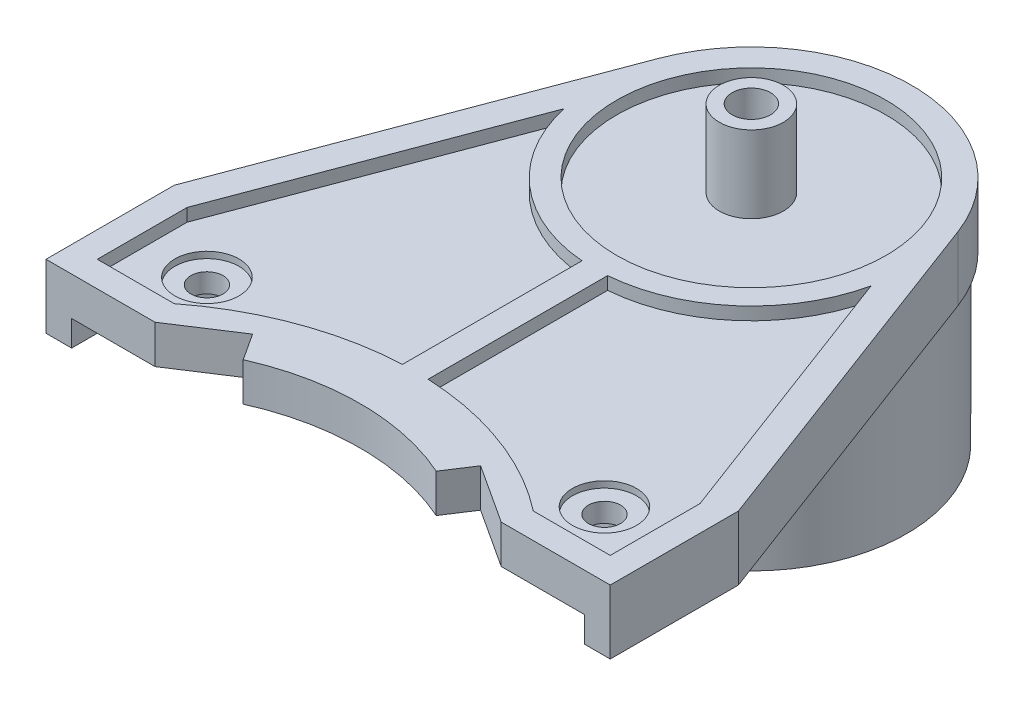
SolidWorks part; units mm, degrees
material "ABS"
ref_plane "Front Plane" through (0, 0, 0) normal (0, 0, 1) x (1, 0, 0)
ref_plane "Top Plane" through (0, 0, 0) normal (0, 1, 0) x (1, 0, 0)
ref_plane "Right Plane" through (0, 0, 0) normal (1, 0, 0) x (0, 0, -1)
sketch "Sketch1" plane through (0, 0, 0) normal (0, 1, 0) x (1, 0, 0)
  line L0 (-22, -33.0049) -> (-13.5, -33.0049)
  line L1 (-13.5, -33.0049) -> (13.5, -33.0049) construction
  line L2 (-22, -33.0049) -> (-22, -23.0049)
  line L3 (0, -30.5) -> (0, 12.5)
  line L4 (-13.5, -33.0049) -> (-8.8902, -30.0049)
  line L5 (0, -55) -> (0, 55) construction
  line L6 (-8.8902, -30.0049) -> (-7.5266, -32.1003)
  line L7 (-11.7009, 4.3977) -> (-22, -23.0049)
  line L8 (11.7009, 4.3977) -> (22, -23.0049)
  line L9 (8.8902, -30.0049) -> (7.5266, -32.1003)
  line L10 (13.5, -33.0049) -> (8.8902, -30.0049)
  line L11 (22, -33.0049) -> (22, -23.0049)
  line L12 (22, -33.0049) -> (13.5, -33.0049)
  arc A0 (11.7009, 4.3977) -> (-11.7009, 4.3977) centre (0, 0) ccw
  arc A2 (7.5266, -32.1003) -> (-7.5266, -32.1003) centre (0, -49) ccw
  point P5 (0, -33.0049)
  point P11 (0, -49)
  dimension "D1" = 25
  dimension "D5" = 18.5
  dimension "D2" = 8.5
  dimension "D3" = 5.5
  dimension "D4" = 10
  dimension "D6" = 13.5
  dimension "D7" = 2.5
  dimension "D8" = 90
  dimension "D9" = 3
  dimension "D11" = 49
extrude "Boss-Extrude1" add sketch "Sketch1" along normal blind 5 contours A2 L3 A0 L7 L2 L0 L4 L6 | A2 L9 L10 L12 L11 L8 A0 L3
sketch "Sketch3" plane through (0, 5, 0) normal (0, 1, 0) x (1, 0, 0)
  circle A0 centre (0, 0) radius 10.5
  dimension "D1" = 21
extrude "Cut-Extrude1" cut sketch "Sketch3" against normal blind 1 contours A0
sketch "Sketch4" plane through (0, 4, 0) normal (0, 1, 0) x (1, 0, 0)
  circle A0 centre (0, 0) radius 2.5
  dimension "D1" = 5
extrude "Boss-Extrude2" add sketch "Sketch4" along normal blind 6
sketch "Sketch5" plane through (0, 10, 0) normal (0, 1, 0) x (1, 0, 0)
  circle A0 centre (0, 0) radius 1.5
  dimension "D1" = 3
extrude "Cut-Extrude2" cut sketch "Sketch5" against normal blind 3
sketch "Sketch6" plane through (0, 5, 0) normal (0, 1, 0) x (1, 0, 0)
  line L0 (1, -26.2091) -> (20, -26.2091) construction
  line L1 (-1, -12.2091) -> (-1, -26.2091)
  line L2 (-1, -26.2091) -> (-20, -26.2091) construction
  line L3 (-20, -24.0049) -> (-20, -31.0049)
  line L4 (-22, -33.0049) -> (-13.5, -33.0049) construction
  line L5 (0, -5.5) -> (0, 5.5) construction
  line L6 (-20, -31.0049) -> (-14, -31.0049)
  line L7 (-20, -24.0049) -> (-11.9651, -2.6266)
  line L8 (-11.7009, 4.3977) -> (-22, -23.0049) construction
  line L9 (20, -24.0049) -> (11.9651, -2.6266)
  line L10 (20, -31.0049) -> (14, -31.0049)
  line L11 (20, -24.0049) -> (20, -31.0049)
  line L12 (1, -12.2091) -> (1, -26.2091)
  arc A0 (-11.9651, -2.6266) -> (-1, -12.2091) centre (0, 0) ccw
  arc A1 (-1, -26.2091) -> (-14, -31.0049) centre (0, -48.9372) ccw
  arc A2 (1, -26.2091) -> (14, -31.0049) centre (0, -48.9372) cw
  arc A3 (11.9651, -2.6266) -> (1, -12.2091) centre (0, 0) cw
  dimension "D10" = 360
  dimension "D8" = 12.25
  dimension "D2" = 22.8384
  dimension "D3" = 14
  dimension "D4" = 19
  dimension "D5" = 7
  dimension "D6" = 2
  dimension "D7" = 6
extrude "Cut-Extrude3" cut sketch "Sketch6" against normal blind 1
sketch "Sketch7" plane through (0, 4, 0) normal (0, 1, 0) x (1, 0, 0)
  line L0 (-22, -33.0049) -> (-13.5, -33.0049) construction
  line L1 (0, -5.5) -> (0, 5.5) construction
  circle A0 centre (-15.5, -26.9549) radius 1.25
  circle A1 centre (15.5, -26.9549) radius 1.25
  dimension "D1" = 2.5
  dimension "D2" = 6.05
  dimension "D3" = 15.5
extrude "Cut-Extrude4" cut sketch "Sketch7" against normal through all
sketch "Sketch8" plane through (0, 4, 0) normal (0, 1, 0) x (1, 0, 0)
  line L0 (-22, -33.0049) -> (-13.5, -33.0049) construction
  line L1 (0, -5.5) -> (0, 5.5) construction
  circle A0 centre (-15.5, -26.9549) radius 2.5
  circle A1 centre (15.5, -26.9549) radius 2.5
  dimension "D1" = 5
  dimension "D2" = 6.05
  dimension "D3" = 15.5
extrude "Cut-Extrude5" cut sketch "Sketch8" against normal blind 0.5
sketch "Sketch9" plane through (0, 0, 0) normal (0, -1, 0) x (1, 0, 0)
  line L0 (0, 30.5) -> (0, 18) construction
  line L1 (0, -5.5) -> (0, 5.5) construction
  line L2 (22, 33.0049) -> (22, 23.0049) construction
  line L3 (22, 33.0049) -> (13.5, 33.0049) construction
  line L4 (20, 33.0049) -> (20, 27.0049)
  line L5 (-20, 33.0049) -> (-20, 27.0049)
  line L7 (20, 33.0049) -> (-20, 33.0049)
  arc A3 (-20, 27.0049) -> (20, 27.0049) centre (0, 44.7125) ccw
  arc A6 (-7.5266, 32.1003) -> (7.5266, 32.1003) centre (0, 49) ccw construction
  dimension "D5" = 0
  dimension "D2" = 2
  dimension "D1" = 0
  dimension "D6" = 12.5
  dimension "D7" = 0
  dimension "D8" = 44.7125
extrude "Cut-Extrude6" cut sketch "Sketch9" against normal blind 2
sketch "Sketch11" plane through (0, 0, 0) normal (0, -1, 0) x (1, 0, 0)
  line L0 (-20, 33.0049) -> (-20, 23.0049) construction
  line L1 (-20, 23.0049) -> (-10.0731, -3.4072)
  line L2 (-11.7009, -4.3977) -> (-22, 23.0049) construction
  line L3 (-20, 23.0049) -> (-20, 25.5296)
  line L4 (0, -5.5) -> (0, 5.5) construction
  line L5 (20, 23.0049) -> (20, 25.5296)
  line L6 (20, 23.0049) -> (10.0731, -3.4072)
  arc A0 (-20, 25.5296) -> (20, 25.5296) centre (0, 44.7125) ccw
  arc A1 (-10.0731, -3.4072) -> (10.0731, -3.4072) centre (0, 0) ccw
  dimension "D1" = 27.7125
  dimension "D2" = 10
  dimension "D3" = 0
extrude "Cut-Extrude7" cut sketch "Sketch11" against normal blind 2
sketch "Sketch12" plane through (0, 2, 0) normal (0, -1, 0) x (1, 0, 0)
  circle A0 centre (0, 0) radius 12.1
  dimension "D1" = 24.2
extrude "Boss-Extrude3" add sketch "Sketch12" along normal blind 15
sketch "Sketch13" plane through (0, -13, 0) normal (0, -1, 0) x (1, 0, 0)
  circle A0 centre (0, 0) radius 2.5
  circle A1 centre (0, 0) radius 10.4
  dimension "D1" = 5
  dimension "D2" = 20.8
extrude "Cut-Extrude8" cut sketch "Sketch13" against normal blind 14
sketch "Sketch14" plane through (0, -13, 0) normal (0, -1, 0) x (1, 0, 0)
  circle A0 centre (0, 0) radius 1.5
  dimension "D1" = 3
extrude "Cut-Extrude9" cut sketch "Sketch14" against normal blind 5
